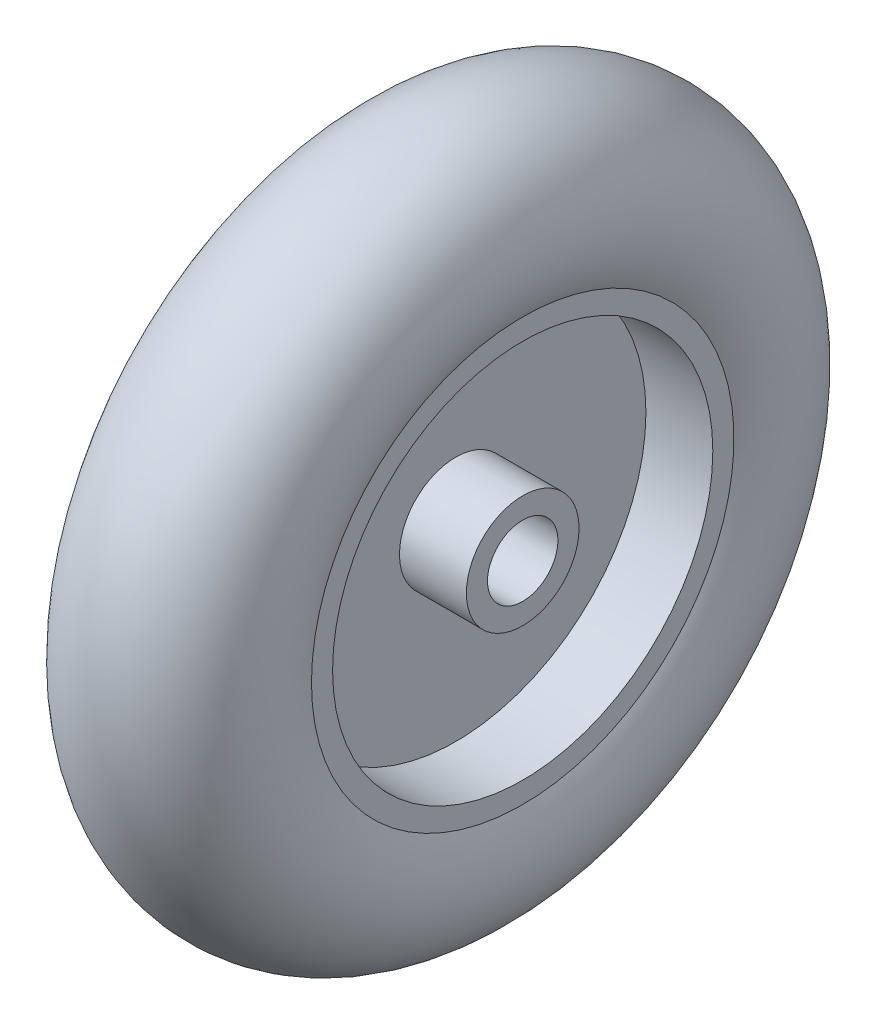
SolidWorks part; units mm, degrees
ref_plane "Front" through (0, 0, 0) normal (0, 0, 1) x (1, 0, 0)
ref_plane "Top" through (0, 0, 0) normal (0, 1, 0) x (1, 0, 0)
ref_plane "Right" through (0, 0, 0) normal (1, 0, 0) x (0, 0, -1)
sketch "Sketch1" plane through (0, 0, 0) normal (0, 1, 0) x (1, 0, 0)
  line L0 (-7.022, 0) -> (6.6806, 0) construction
  line L5 (-12, 8) -> (-2.5, 8)
  line L6 (-12, 5) -> (12, 5)
  line L7 (-12, 5) -> (-12, 8)
  line L9 (12, 5) -> (12, 8)
  line L10 (-12, 27) -> (-2.5, 27)
  line L11 (-12, 27) -> (-12, 30)
  line L13 (12, 27) -> (12, 30)
  line L14 (-2.5, 8) -> (-2.5, 27)
  line L23 (2.5, 27) -> (2.5, 8)
  line L24 (2.5, 27) -> (12, 27)
  line L25 (2.5, 8) -> (12, 8)
  arc A0 (12, 30) -> (-12, 30) centre (0, 36.4) ccw
  point P1 (-12, 27.4992)
  point P2 (12, 27.4992)
  point P4 (0, 0)
  point P17 (0, 5)
  point P22 (-12, 28.5)
  dimension "D1" = 50
  dimension "D2" = 30
  dimension "D3" = 24
  dimension "D4" = 3
revolve "Revolve1" add sketch "Sketch1" angle 360 about L0
